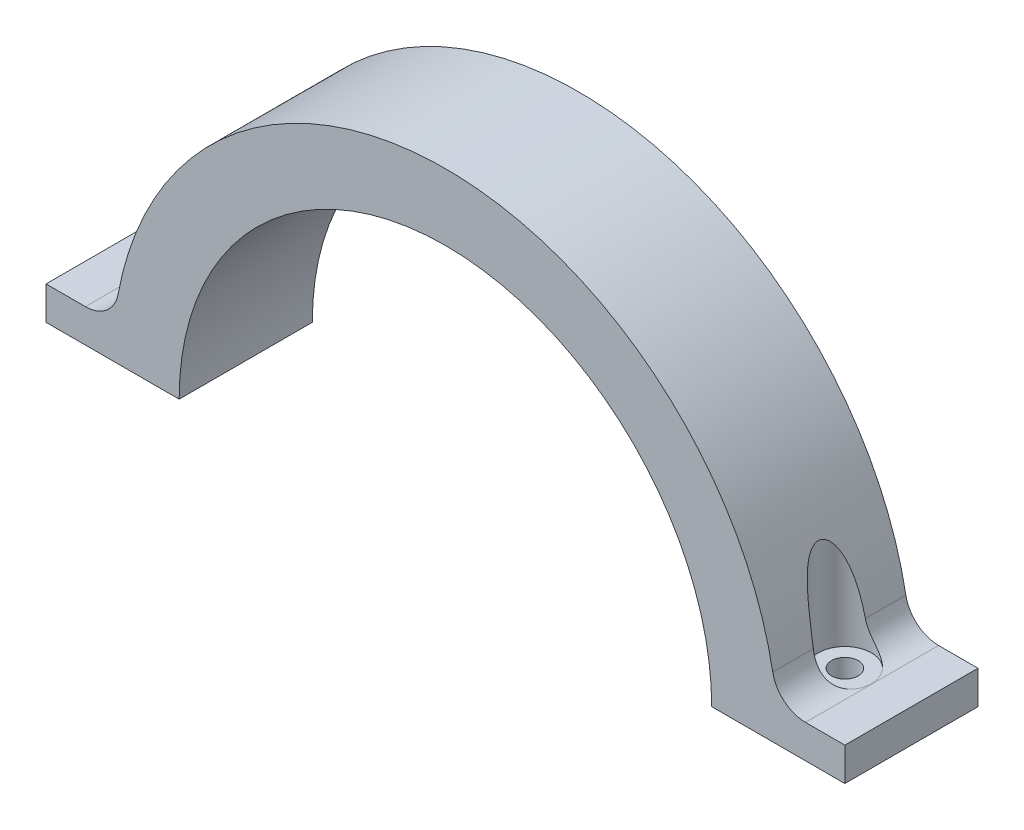
SolidWorks part; units mm, degrees
ref_plane "Front Plane" through (0, 0, 0) normal (0, 0, 1) x (1, 0, 0)
ref_plane "Top Plane" through (0, 0, 0) normal (0, 1, 0) x (1, 0, 0)
ref_plane "Right Plane" through (0, 0, 0) normal (1, 0, 0) x (0, 0, -1)
sketch "Sketch1" plane through (0, 0, 0) normal (0, 0, 1) x (1, 0, 0)
  line L1 (-40, 0) -> (-60, 0)
  line L2 (-60, 0) -> (-60, 5)
  line L3 (-60, 5) -> (-54.0833, 5)
  line L4 (0, 50) -> (0, 0) construction
  line L5 (0, 50) -> (0, 40)
  arc A0 (0, 40) -> (-40, 0) centre (0, 0) ccw
  arc A1 (0, 50) -> (-49.1666, 9.0909) centre (0, 0) ccw
  arc A2 (40, 0) -> (-40, 0) centre (0, 0) ccw construction
  arc A3 (50, 0) -> (-50, 0) centre (0, 0) ccw construction
  arc A4 (-54.0833, 5) -> (-49.1666, 9.0909) centre (-54.0833, 10) ccw
  dimension "D1" = 10
  dimension "D4" = 5
  dimension "D5" = 40
  dimension "D2" = 20
  dimension "D3" = 5
extrude "Boss-Extrude1" add sketch "Sketch1" along normal blind 20 contours L5 A1 L1 A0 | A1 L3 L2 L1
sketch "Sketch2" plane through (0, 0, 0) normal (0, -1, 0) x (1, 0, 0)
  line L0 (-60, 20) -> (-40, 0)
  line L1 (-40, 0) -> (-60, 0) construction
  line L2 (-40, 20) -> (-60, 20) construction
  circle A0 centre (-50, 10) radius 2
  dimension "D1" = 45
extrude "Cut-Extrude1" cut sketch "Sketch2" against normal blind 20 contours L0 A0 | L0 A0
sketch "Sketch4" plane through (0, 5, 0) normal (0, 1, 0) x (1, 0, 0)
  circle A0 centre (-50, -10) radius 2
  circle A1 centre (-50, -10) radius 4
extrude "Cut-Extrude2" cut sketch "Sketch4" along normal blind 37
mirror "Mirror1" about plane through (0, 0, 20) normal (1, 0, 0) of "Cut-Extrude2", "Boss-Extrude1", "Cut-Extrude1"
